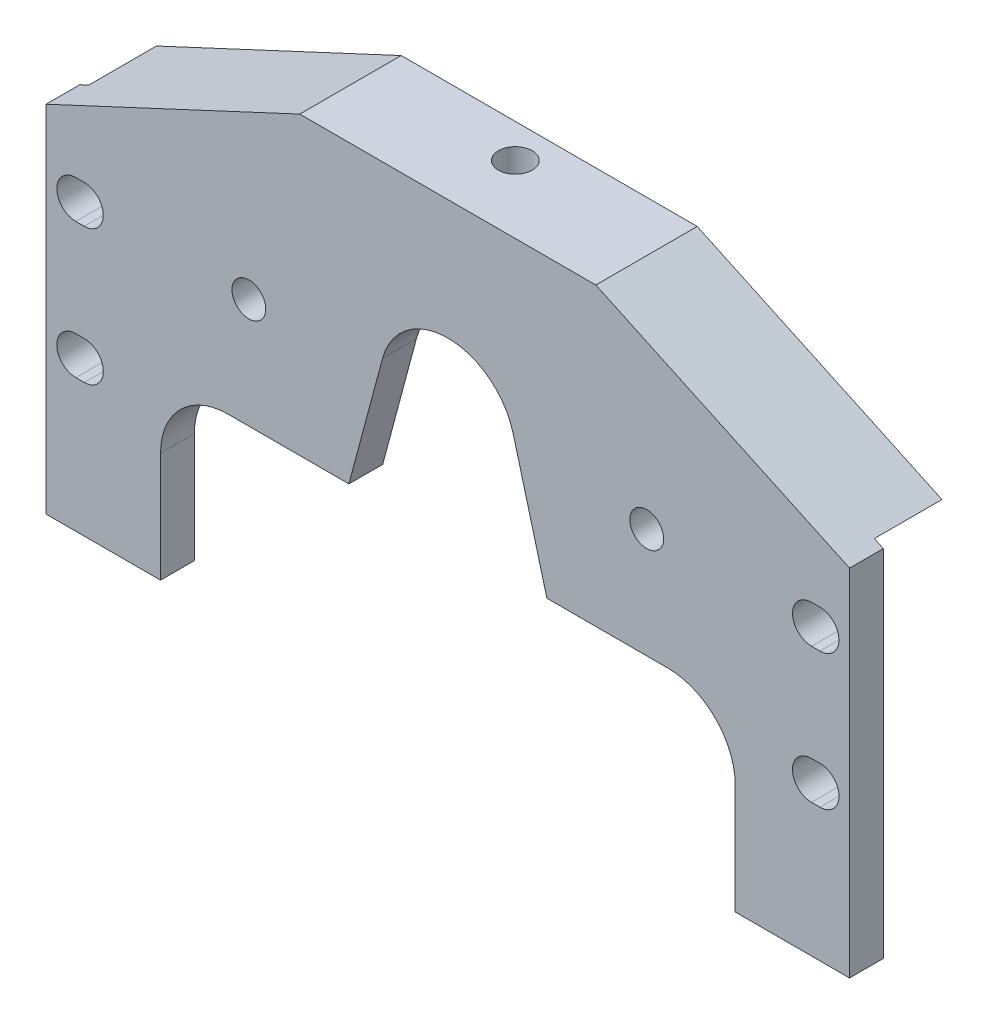
SolidWorks part; units mm, degrees
material "AISI 1018 Steel, Cold Rolled"
ref_plane "Front" through (0, 0, 0) normal (0, 0, 1) x (1, 0, 0)
ref_plane "Top" through (0, 0, 0) normal (0, 1, 0) x (1, 0, 0)
ref_plane "Right" through (0, 0, 0) normal (1, 0, 0) x (0, 0, -1)
sketch "Sketch1" plane through (0, 0, 0) normal (0, 0, 1) x (1, 0, 0)
  line L0 (58.1216, 111.0985) -> (-37.2017, 66.6485)
  line L2 (264.6574, 66.6485) -> (169.3341, 111.0985)
  line L3 (58.1216, 111.0985) -> (169.3341, 111.0985)
  line L4 (264.6574, -66.7015) -> (264.6574, 66.6485)
  line L5 (-37.2017, 66.6485) -> (-37.2017, -66.7015)
  line L6 (-37.2017, -66.7015) -> (264.6574, -66.7015)
  dimension "D1" = 115
  dimension "D2" = 177.8
  dimension "D3" = 133.35
  dimension "D4" = 115
  dimension "D5" = 133.35
  dimension "D6" = 301.8591
extrude "Base-Extrude" add sketch "Sketch1" along normal blind 12.7
hole_wizard "9/16 (0.5625) Diameter Hole1" positions "Sketch7" profile "Sketch6" hole size "9/16" standard "Ansi Inch" end condition through all
sketch "Sketch7" plane through (0, 0, 12.7) normal (0, 0, 1) x (1, 0, 0)
  line L0 (264.6574, -66.7015) -> (264.6574, 66.6485) construction
  line L3 (-37.2017, -66.7015) -> (264.6574, -66.7015) construction
  point P0 (251.9574, -9.5515)
  point P7 (251.9574, 41.2485)
  dimension "D1" = 12.7
  dimension "D2" = 57.15
  dimension "D3" = 50.8
  dimension "D4" = 12.7
sketch "Sketch6" plane through (251.9574, -9.5515, 12.7) normal (1, 0, 0) x (0, -1, 0)
  line L0 (0, 0) -> (0, 12.7)
  line L1 (0, 12.7) -> (7.1437, 12.7)
  line L2 (7.1437, 12.7) -> (7.1437, 0)
  line L5 (7.1437, 0) -> (0, 0)
  line L11 (0, -6.35) -> (0, 107.95) construction
  dimension "Thru Hole Dia." = 14.2875
  dimension "Thru Hole Depth" = 12.7
sketch "Sketch8" plane through (0, 0, 12.7) normal (0, 0, 1) x (1, 0, 0)
  line L2 (12.7, -50.8) -> (12.7, 140.8912) construction
  line L3 (5.8183, -25.4) -> (5.8183, -66.7015)
  line L4 (150.9565, 0) -> (196.3183, 0)
  line L5 (-37.2017, -66.7015) -> (264.6574, -66.7015) construction
  line L6 (5.8183, -66.7015) -> (221.7183, -66.7015)
  line L7 (-37.2017, 66.6485) -> (-37.2017, -66.7015) construction
  line L8 (221.7183, -66.7015) -> (221.7183, -25.4)
  line L11 (31.2183, 0) -> (76.5801, 0)
  line L13 (150.9565, 0) -> (138.3028, 47.2241)
  line L14 (89.2338, 47.2241) -> (76.5801, 0)
  arc A0 (89.2338, 47.2241) -> (138.3028, 47.2241) centre (113.7683, 40.6501) cw
  arc A1 (31.2183, 0) -> (5.8183, -25.4) centre (31.2183, -25.4) ccw
  arc A2 (221.7183, -25.4) -> (196.3183, 0) centre (196.3183, -25.4) ccw
  dimension "D1" = 25.4
  dimension "D5" = 25.4
  dimension "D3" = 107.95
  dimension "D2" = 150.97
  dimension "D4" = 107.95
extrude "Cut-Extrude1" cut sketch "Sketch8" against normal up to next
ref_plane "Plane4" through (-37.2017, 0, 0) normal (1, 0, 0) x (0, 0, -1)
ref_plane "Plane5" through (113.7683, 0, 0) normal (1, 0, 0) x (0, 0, -1)
mirror "Mirror3" about plane through (113.7683, 0, 0) normal (1, 0, 0) of "9/16 (0.5625) Diameter Hole1"
sketch "Sketch10" plane through (0, 0, 0) normal (0, 0, -1) x (-1, 0, 0)
  line L0 (-169.3341, 111.0985) -> (-58.1216, 111.0985) construction
  line L1 (-169.3341, 111.0985) -> (-58.1216, 111.0985)
  line L2 (-58.1216, 111.0985) -> (37.2017, 66.6485) construction
  line L3 (-58.1216, 111.0985) -> (33.8245, 68.2233)
  line L4 (-264.6574, 66.6485) -> (-169.3341, 111.0985) construction
  line L5 (-261.2802, 68.2233) -> (-169.3341, 111.0985)
  line L6 (-261.2802, 68.2233) -> (33.8245, 68.2233)
  dimension "D1" = 42.8752
extrude "Boss-Extrude1" add sketch "Sketch10" along normal blind 25.4
hole_wizard "1/2-20 Tapped Hole1" positions "Sketch12" profile "Sketch11" tap size "1/2-20" standard "Ansi Inch" end condition through all
sketch "Sketch12" plane through (0, 111.0985, 0) normal (0, 1, 0) x (-1, 0, 0)
  line L0 (-58.1216, 12.7) -> (-58.1216, -25.4) construction
  line L1 (-58.1216, -25.4) -> (-169.3341, -25.4) construction
  point P0 (-113.6968, -12.7)
  dimension "D1" = 55.5752
  dimension "D2" = 12.7
sketch "Sketch11" plane through (113.6968, 111.0985, -12.7) normal (1, 0, 0) x (0, 0, 1)
  line L0 (0, 0) -> (0, 177.8)
  line L1 (0, 177.8) -> (6.35, 177.8)
  line L2 (6.35, 177.8) -> (6.35, 0)
  line L5 (6.35, 0) -> (0, 0)
  line L11 (0, -6.35) -> (0, 107.95) construction
  dimension "Thread Major Dia." = 12.7
  dimension "Thru Tap Drill Depth" = 177.8
sketch "Sketch13" plane through (0, 0, 12.7) normal (0, 0, 1) x (1, 0, 0)
  line L0 (250.3699, -2.4078) -> (253.5449, -2.4078)
  line L1 (253.5449, -16.6953) -> (250.3699, -16.6953)
  arc A1 (250.3699, -2.4078) -> (250.3699, -16.6953) centre (250.3699, -9.5515) ccw
  arc A2 (253.5449, -16.6953) -> (253.5449, -2.4078) centre (253.5449, -9.5515) ccw
extrude "Cut-Extrude2" cut sketch "Sketch13" against normal through all
sketch "Sketch14" plane through (0, 0, 12.7) normal (0, 0, 1) x (1, 0, 0)
  line L0 (253.5322, 48.3922) -> (250.3826, 48.3922)
  line L1 (250.3826, 34.1047) -> (253.5322, 34.1047)
  arc A2 (253.5322, 34.1047) -> (253.5322, 48.3922) centre (253.5322, 41.2485) ccw
  arc A3 (250.3826, 48.3922) -> (250.3826, 34.1047) centre (250.3826, 41.2485) ccw
extrude "Cut-Extrude3" cut sketch "Sketch14" against normal through all
mirror "Mirror4" about plane through (113.7683, 0, 0) normal (1, 0, 0) of "Cut-Extrude3", "Cut-Extrude2"
hole_wizard "1/2-20 Tapped Hole2" positions "Sketch16" profile "Sketch15" tap size "1/2-20" standard "Ansi Inch" end condition through all
sketch "Sketch16" plane through (0, 0, 12.7) normal (0, 0, 1) x (1, 0, 0)
  line L0 (-37.2017, -20.955) -> (-37.2017, 20.955) construction
  line L1 (-37.2017, -66.7015) -> (5.8183, -66.7015) construction
  line L2 (264.6574, -66.7015) -> (264.6574, 66.6485) construction
  line L3 (221.7183, -66.7015) -> (264.6574, -66.7015) construction
  point P0 (38.9983, 41.2485)
  point P5 (188.4574, 41.2485)
  dimension "D1" = 76.2
  dimension "D2" = 107.95
  dimension "D3" = 76.2
  dimension "D4" = 107.95
sketch "Sketch15" plane through (38.9983, 41.2485, 12.7) normal (1, 0, 0) x (0, -1, 0)
  line L0 (0, 0) -> (0, 38.1)
  line L1 (0, 38.1) -> (6.35, 38.1)
  line L2 (6.35, 38.1) -> (6.35, 0)
  line L5 (6.35, 0) -> (0, 0)
  line L11 (0, -6.35) -> (0, 107.95) construction
  dimension "Thread Major Dia." = 12.7
  dimension "Thru Tap Drill Depth" = 38.1
sketch "Sketch17" plane through (0, 0, -25.4) normal (0, 0, -1) x (-1, 0, 0)
  line L0 (-261.2802, 68.2233) -> (33.8245, 68.2233) construction
  line L1 (-132.7779, 68.2233) -> (-94.6779, 68.2233)
  line L3 (-123.2529, 96.7983) -> (-104.2029, 96.7983)
  line L5 (-132.7779, 87.2733) -> (-132.7779, 68.2233)
  line L6 (-94.6779, 87.2733) -> (-94.6779, 68.2233)
  arc A0 (-123.2529, 96.7983) -> (-132.7779, 87.2733) centre (-123.2529, 87.2733) ccw
  arc A1 (-94.6779, 87.2733) -> (-104.2029, 96.7983) centre (-104.2029, 87.2733) ccw
  dimension "D1" = 9.525
extrude "Cut-Extrude4" cut sketch "Sketch17" against normal blind 25.4
ref_point "Point1"
ref_plane "CENTER Plane" through (113.7288, 0, 0) normal (1, 0, 0) x (0, 0, -1)
